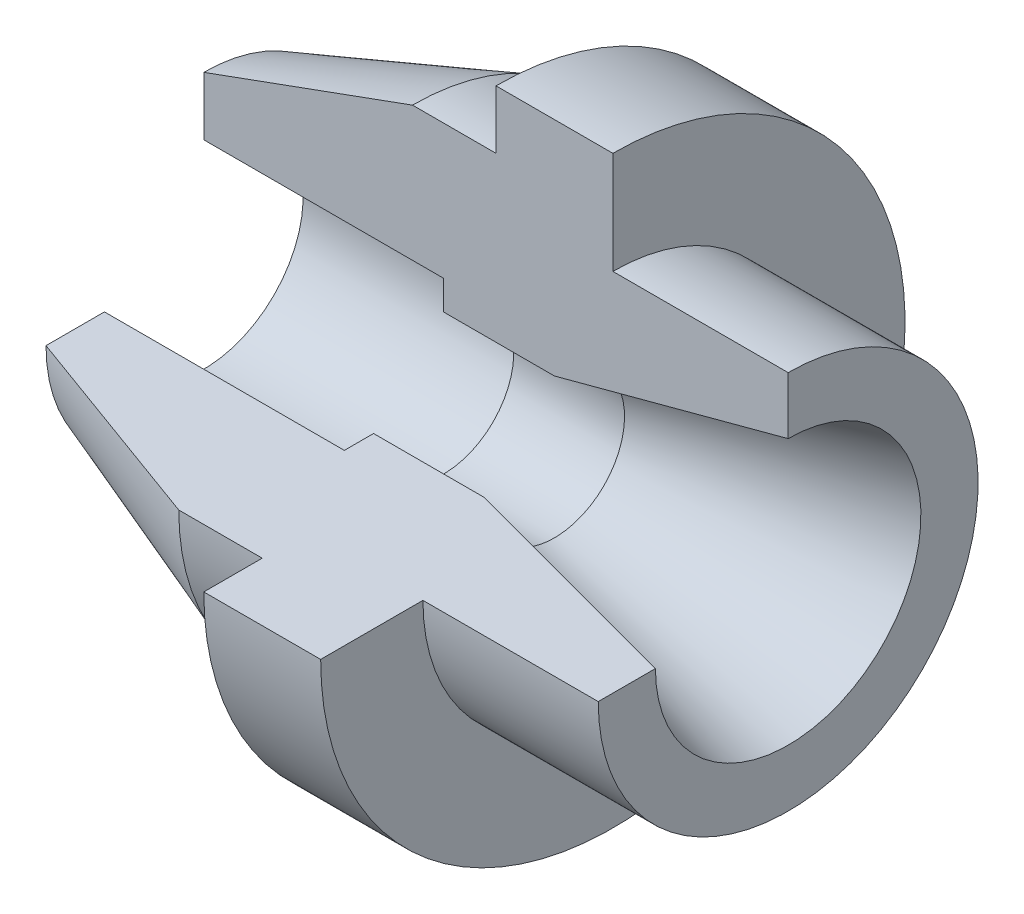
SolidWorks part; units mm, degrees
ref_plane "Front Plane" through (0, 0, 0) normal (0, 0, 1) x (1, 0, 0)
ref_plane "Top Plane" through (0, 0, 0) normal (0, 1, 0) x (1, 0, 0)
ref_plane "Right Plane" through (0, 0, 0) normal (1, 0, 0) x (0, 0, -1)
ref_axis "Axis2" through (88.99, 0, 0) along (-1, 0, 0)
sketch "Sketch2" plane through (0, 0, 0) normal (0, 0, 1) x (1, 0, 0)
  line L0 (-54.5225, 27) -> (-54.5225, 0)
  line L1 (88.99, 0) -> (-88.99, 0) construction
  line L2 (-54.5225, 0) -> (45.4775, 0)
  line L4 (-54.5225, 27) -> (-18.8053, 40)
  line L5 (-18.8053, 40) -> (-4.5225, 40)
  line L6 (-4.5225, 40) -> (-4.5225, 50)
  line L7 (-4.5225, 50) -> (15.4775, 50)
  line L8 (15.4775, 50) -> (15.4775, 32.5)
  line L9 (15.4775, 32.5) -> (45.4775, 32.5)
  line L11 (45.4775, 32.5) -> (45.4775, 0)
  dimension "D2" = 100
  dimension "D3" = 70
  dimension "D4" = 27
  dimension "D5" = 40
  dimension "D6" = 32.5
  dimension "D9" = 30
  dimension "D10" = 20
  dimension "D13" = 50
revolve "Revolve1" add sketch "Sketch2" angle 270 about axis through (88.99, 0, 0) along (-1, 0, 0)
sketch "Sketch3" plane through (0, 0, 0) normal (0, 0, 1) x (1, 0, 0)
  line L0 (-54.5225, 0) -> (45.4775, 0)
  line L1 (45.4775, 0) -> (45.4775, 22.718)
  line L2 (45.4775, 32.5) -> (45.4775, 0) construction
  line L3 (45.4775, 22.718) -> (5.4775, 12)
  line L4 (5.4775, 12) -> (-13.4717, 12)
  line L5 (-13.4717, 12) -> (-13.4717, 17)
  line L6 (-13.4717, 17) -> (-54.5225, 17)
  line L8 (-54.5225, 17) -> (-54.5225, 0)
  point P4 (-93.3559, 21.5492)
  dimension "D1" = 15
  dimension "D2" = 60
  dimension "D3" = 12
  dimension "D4" = 17
revolve "Cut-Revolve1" cut sketch "Sketch3" angle 360 about L0
